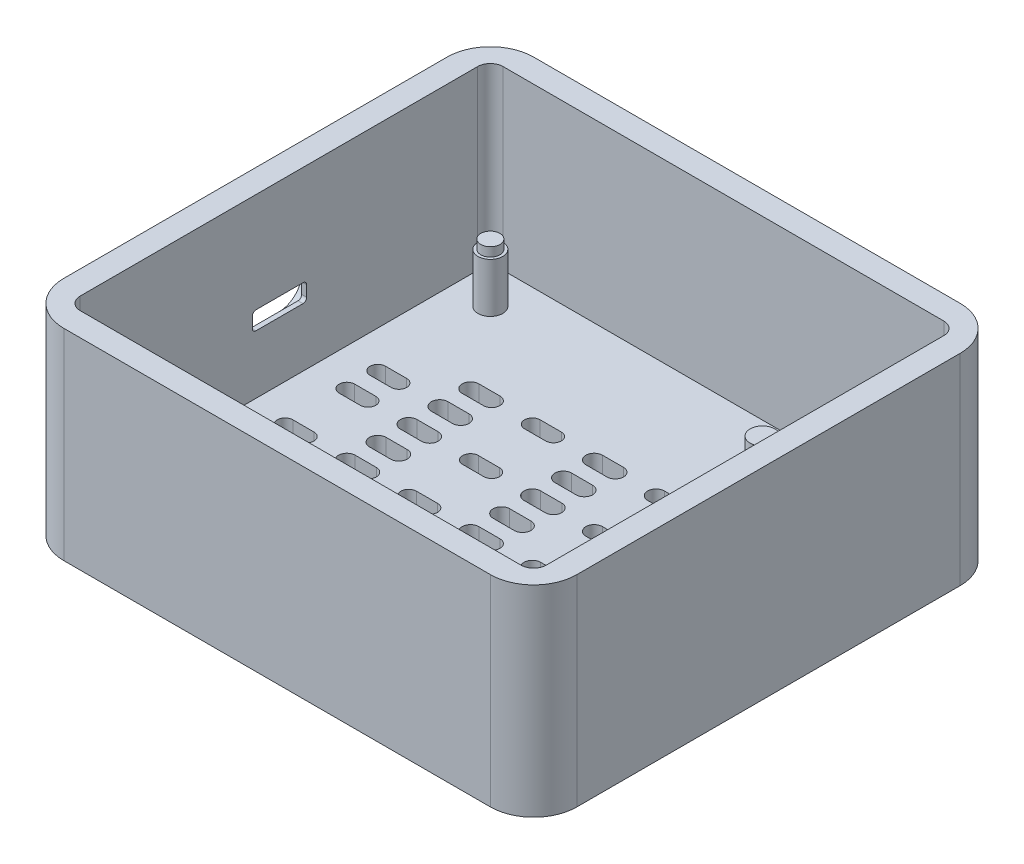
SolidWorks part; units mm, degrees
ref_plane "前视基准面" through (0, 0, 0) normal (0, 0, 1) x (1, 0, 0)
ref_plane "上视基准面" through (0, 0, 0) normal (0, 1, 0) x (1, 0, 0)
ref_plane "右视基准面" through (0, 0, 0) normal (1, 0, 0) x (0, 0, -1)
other "Configuration Table"
sketch "草图1" plane through (0, 0, 0) normal (0, 1, 0) x (1, 0, 0)
  line L1 (-34.5, 34) -> (34.5, 34)
  line L2 (-37.5, 31) -> (-37.5, -31)
  line L3 (-34.5, -34) -> (34.5, -34)
  line L4 (37.5, 31) -> (37.5, -31)
  line L5 (-37.5, 34) -> (37.5, -34) construction
  line L6 (-37.5, -34) -> (37.5, 34) construction
  arc A0 (-34.5, 34) -> (-37.5, 31) centre (-34.5, 31) ccw
  arc A1 (-37.5, -31) -> (-34.5, -34) centre (-34.5, -31) ccw
  arc A2 (34.5, -34) -> (37.5, -31) centre (34.5, -31) ccw
  arc A3 (34.5, 34) -> (37.5, 31) centre (34.5, 31) cw
  point P0 (0, 0)
  dimension "D3" = 3
  dimension "D4" = 3
  dimension "D1" = 75
  dimension "D2" = 68
extrude "凸台-拉伸1" add sketch "草图1" along normal blind 4
sketch "草图2" plane through (0, 4, 0) normal (0, 1, 0) x (1, 0, 0)
  line L0 (-1.709, 0) -> (1.709, 0) construction
  line L1 (-1.709, 1.3428) -> (1.709, 1.3428)
  line L2 (-1.709, -1.3428) -> (1.709, -1.3428)
  line L6 (18.291, 0) -> (21.709, 0) construction
  line L7 (18.291, 1.3428) -> (21.709, 1.3428)
  line L8 (18.291, -1.3428) -> (21.709, -1.3428)
  line L15 (-21.709, 0) -> (-18.291, 0) construction
  line L16 (-21.709, 1.3428) -> (-18.291, 1.3428)
  line L17 (-21.709, -1.3428) -> (-18.291, -1.3428)
  line L21 (-1.709, -5) -> (1.709, -5) construction
  line L22 (-1.709, -3.6572) -> (1.709, -3.6572)
  line L23 (-1.709, -6.3428) -> (1.709, -6.3428)
  line L24 (8.291, -5) -> (11.709, -5) construction
  line L25 (8.291, -3.6572) -> (11.709, -3.6572)
  line L26 (8.291, -6.3428) -> (11.709, -6.3428)
  line L27 (18.291, -5) -> (21.709, -5) construction
  line L28 (18.291, -3.6572) -> (21.709, -3.6572)
  line L29 (18.291, -6.3428) -> (21.709, -6.3428)
  line L30 (28.291, -5) -> (31.709, -5) construction
  line L31 (28.291, -3.6572) -> (31.709, -3.6572)
  line L32 (28.291, -6.3428) -> (31.709, -6.3428)
  line L33 (-11.709, -5) -> (-8.291, -5) construction
  line L34 (-11.709, -3.7386) -> (-8.291, -3.7386)
  line L35 (-11.709, -6.2614) -> (-8.291, -6.2614)
  line L36 (-21.709, -5) -> (-18.291, -5) construction
  line L37 (-21.709, -3.6572) -> (-18.291, -3.6572)
  line L38 (-21.709, -6.3428) -> (-18.291, -6.3428)
  line L39 (-31.709, -5) -> (-28.291, -5) construction
  line L40 (-31.709, -3.7386) -> (-28.291, -3.7386)
  line L41 (-31.709, -6.2614) -> (-28.291, -6.2614)
  line L42 (-1.709, -10) -> (1.709, -10) construction
  line L43 (-1.709, -8.6572) -> (1.709, -8.6572)
  line L44 (-1.709, -11.3428) -> (1.709, -11.3428)
  line L48 (18.291, -10) -> (21.709, -10) construction
  line L49 (18.291, -8.6572) -> (21.709, -8.6572)
  line L50 (18.291, -11.3428) -> (21.709, -11.3428)
  line L51 (28.291, -10) -> (31.709, -10) construction
  line L52 (28.291, -8.6572) -> (31.709, -8.6572)
  line L53 (28.291, -11.3428) -> (31.709, -11.3428)
  line L57 (-21.709, -10) -> (-18.291, -10) construction
  line L58 (-21.709, -8.6572) -> (-18.291, -8.6572)
  line L59 (-21.709, -11.3428) -> (-18.291, -11.3428)
  line L60 (-31.709, -10) -> (-28.291, -10) construction
  line L61 (-31.709, -8.7386) -> (-28.291, -8.7386)
  line L62 (-31.709, -11.2614) -> (-28.291, -11.2614)
  line L63 (-1.709, -15) -> (1.709, -15) construction
  line L64 (-1.709, -13.6572) -> (1.709, -13.6572)
  line L65 (-1.709, -16.3428) -> (1.709, -16.3428)
  line L66 (8.291, -15) -> (11.709, -15) construction
  line L67 (8.291, -13.6572) -> (11.709, -13.6572)
  line L68 (8.291, -16.3428) -> (11.709, -16.3428)
  line L69 (18.291, -15) -> (21.709, -15) construction
  line L70 (18.291, -13.6572) -> (21.709, -13.6572)
  line L71 (18.291, -16.3428) -> (21.709, -16.3428)
  line L75 (-11.709, -15) -> (-8.291, -15) construction
  line L76 (-11.709, -13.7386) -> (-8.291, -13.7386)
  line L77 (-11.709, -16.2614) -> (-8.291, -16.2614)
  line L78 (-21.709, -15) -> (-18.291, -15) construction
  line L79 (-21.709, -13.6572) -> (-18.291, -13.6572)
  line L80 (-21.709, -16.3428) -> (-18.291, -16.3428)
  line L84 (-1.709, 5) -> (1.709, 5) construction
  line L85 (-1.709, 6.3428) -> (1.709, 6.3428)
  line L86 (-1.709, 3.6572) -> (1.709, 3.6572)
  line L87 (8.291, 5) -> (11.709, 5) construction
  line L88 (8.291, 6.3428) -> (11.709, 6.3428)
  line L89 (8.291, 3.6572) -> (11.709, 3.6572)
  line L90 (18.291, 5) -> (21.709, 5) construction
  line L91 (18.291, 6.3428) -> (21.709, 6.3428)
  line L92 (18.291, 3.6572) -> (21.709, 3.6572)
  line L93 (28.291, 5) -> (31.709, 5) construction
  line L94 (28.291, 6.3428) -> (31.709, 6.3428)
  line L95 (28.291, 3.6572) -> (31.709, 3.6572)
  line L96 (-11.709, 5) -> (-8.291, 5) construction
  line L97 (-11.709, 6.2614) -> (-8.291, 6.2614)
  line L98 (-11.709, 3.7386) -> (-8.291, 3.7386)
  line L99 (-21.709, 5) -> (-18.291, 5) construction
  line L100 (-21.709, 6.3428) -> (-18.291, 6.3428)
  line L101 (-21.709, 3.6572) -> (-18.291, 3.6572)
  line L102 (-31.709, 5) -> (-28.291, 5) construction
  line L103 (-31.709, 6.2614) -> (-28.291, 6.2614)
  line L104 (-31.709, 3.7386) -> (-28.291, 3.7386)
  line L105 (-1.709, 10) -> (1.709, 10) construction
  line L106 (-1.709, 11.3428) -> (1.709, 11.3428)
  line L107 (-1.709, 8.6572) -> (1.709, 8.6572)
  line L111 (18.291, 10) -> (21.709, 10) construction
  line L112 (18.291, 11.3428) -> (21.709, 11.3428)
  line L113 (18.291, 8.6572) -> (21.709, 8.6572)
  line L114 (28.291, 10) -> (31.709, 10) construction
  line L115 (28.291, 11.3428) -> (31.709, 11.3428)
  line L116 (28.291, 8.6572) -> (31.709, 8.6572)
  line L120 (-21.709, 10) -> (-18.291, 10) construction
  line L121 (-21.709, 11.3428) -> (-18.291, 11.3428)
  line L122 (-21.709, 8.6572) -> (-18.291, 8.6572)
  line L123 (-31.709, 10) -> (-28.291, 10) construction
  line L124 (-31.709, 11.2614) -> (-28.291, 11.2614)
  line L125 (-31.709, 8.7386) -> (-28.291, 8.7386)
  line L126 (-1.709, 15) -> (1.709, 15) construction
  line L127 (-1.709, 16.3428) -> (1.709, 16.3428)
  line L128 (-1.709, 13.6572) -> (1.709, 13.6572)
  line L129 (8.291, 15) -> (11.709, 15) construction
  line L130 (8.291, 16.3428) -> (11.709, 16.3428)
  line L131 (8.291, 13.6572) -> (11.709, 13.6572)
  line L132 (18.291, 15) -> (21.709, 15) construction
  line L133 (18.291, 16.3428) -> (21.709, 16.3428)
  line L134 (18.291, 13.6572) -> (21.709, 13.6572)
  line L138 (-11.709, 15) -> (-8.291, 15) construction
  line L139 (-11.709, 16.2614) -> (-8.291, 16.2614)
  line L140 (-11.709, 13.7386) -> (-8.291, 13.7386)
  line L141 (-21.709, 15) -> (-18.291, 15) construction
  line L142 (-21.709, 16.3428) -> (-18.291, 16.3428)
  line L143 (-21.709, 13.6572) -> (-18.291, 13.6572)
  line L188 (28.291, 0) -> (31.709, 0) construction
  line L189 (28.291, 1.3428) -> (31.709, 1.3428)
  line L190 (28.291, -1.3428) -> (31.709, -1.3428)
  line L191 (8.291, 0) -> (11.709, 0) construction
  line L192 (8.291, 1.3428) -> (11.709, 1.3428)
  line L193 (8.291, -1.3428) -> (11.709, -1.3428)
  line L194 (-11.709, 0) -> (-8.291, 0) construction
  line L195 (-11.709, 1.3428) -> (-8.291, 1.3428)
  line L196 (-11.709, -1.3428) -> (-8.291, -1.3428)
  line L197 (-31.709, 0) -> (-28.291, 0) construction
  line L198 (-31.709, 1.3428) -> (-28.291, 1.3428)
  line L199 (-31.709, -1.3428) -> (-28.291, -1.3428)
  line L200 (28.291, 0) -> (31.709, 0) construction
  line L201 (28.291, 1.3428) -> (31.709, 1.3428)
  line L202 (28.291, -1.3428) -> (31.709, -1.3428)
  line L203 (8.291, 0) -> (11.709, 0) construction
  line L204 (8.291, 1.3428) -> (11.709, 1.3428)
  line L205 (8.291, -1.3428) -> (11.709, -1.3428)
  line L206 (-11.709, 0) -> (-8.291, 0) construction
  line L207 (-11.709, 1.3428) -> (-8.291, 1.3428)
  line L208 (-11.709, -1.3428) -> (-8.291, -1.3428)
  line L209 (-31.709, 0) -> (-28.291, 0) construction
  line L210 (-31.709, 1.3428) -> (-28.291, 1.3428)
  line L211 (-31.709, -1.3428) -> (-28.291, -1.3428)
  arc A0 (-1.709, 1.3428) -> (-1.709, -1.3428) centre (-1.709, 0) ccw
  arc A1 (1.709, -1.3428) -> (1.709, 1.3428) centre (1.709, 0) ccw
  arc A4 (18.291, 1.3428) -> (18.291, -1.3428) centre (18.291, 0) ccw
  arc A5 (21.709, -1.3428) -> (21.709, 1.3428) centre (21.709, 0) ccw
  arc A10 (-21.709, 1.3428) -> (-21.709, -1.3428) centre (-21.709, 0) ccw
  arc A11 (-18.291, -1.3428) -> (-18.291, 1.3428) centre (-18.291, 0) ccw
  arc A14 (-1.709, -3.6572) -> (-1.709, -6.3428) centre (-1.709, -5) ccw
  arc A15 (1.709, -6.3428) -> (1.709, -3.6572) centre (1.709, -5) ccw
  arc A16 (8.291, -3.6572) -> (8.291, -6.3428) centre (8.291, -5) ccw
  arc A17 (11.709, -6.3428) -> (11.709, -3.6572) centre (11.709, -5) ccw
  arc A18 (18.291, -3.6572) -> (18.291, -6.3428) centre (18.291, -5) ccw
  arc A19 (21.709, -6.3428) -> (21.709, -3.6572) centre (21.709, -5) ccw
  arc A20 (28.291, -3.6572) -> (28.291, -6.3428) centre (28.291, -5) ccw
  arc A21 (31.709, -6.3428) -> (31.709, -3.6572) centre (31.709, -5) ccw
  arc A22 (-11.709, -3.7386) -> (-11.709, -6.2614) centre (-11.709, -5) ccw
  arc A23 (-8.291, -6.2614) -> (-8.291, -3.7386) centre (-8.291, -5) ccw
  arc A24 (-21.709, -3.6572) -> (-21.709, -6.3428) centre (-21.709, -5) ccw
  arc A25 (-18.291, -6.3428) -> (-18.291, -3.6572) centre (-18.291, -5) ccw
  arc A26 (-31.709, -3.7386) -> (-31.709, -6.2614) centre (-31.709, -5) ccw
  arc A27 (-28.291, -6.2614) -> (-28.291, -3.7386) centre (-28.291, -5) ccw
  arc A28 (-1.709, -8.6572) -> (-1.709, -11.3428) centre (-1.709, -10) ccw
  arc A29 (1.709, -11.3428) -> (1.709, -8.6572) centre (1.709, -10) ccw
  arc A32 (18.291, -8.6572) -> (18.291, -11.3428) centre (18.291, -10) ccw
  arc A33 (21.709, -11.3428) -> (21.709, -8.6572) centre (21.709, -10) ccw
  arc A34 (28.291, -8.6572) -> (28.291, -11.3428) centre (28.291, -10) ccw
  arc A35 (31.709, -11.3428) -> (31.709, -8.6572) centre (31.709, -10) ccw
  arc A38 (-21.709, -8.6572) -> (-21.709, -11.3428) centre (-21.709, -10) ccw
  arc A39 (-18.291, -11.3428) -> (-18.291, -8.6572) centre (-18.291, -10) ccw
  arc A40 (-31.709, -8.7386) -> (-31.709, -11.2614) centre (-31.709, -10) ccw
  arc A41 (-28.291, -11.2614) -> (-28.291, -8.7386) centre (-28.291, -10) ccw
  arc A42 (-1.709, -13.6572) -> (-1.709, -16.3428) centre (-1.709, -15) ccw
  arc A43 (1.709, -16.3428) -> (1.709, -13.6572) centre (1.709, -15) ccw
  arc A44 (8.291, -13.6572) -> (8.291, -16.3428) centre (8.291, -15) ccw
  arc A45 (11.709, -16.3428) -> (11.709, -13.6572) centre (11.709, -15) ccw
  arc A46 (18.291, -13.6572) -> (18.291, -16.3428) centre (18.291, -15) ccw
  arc A47 (21.709, -16.3428) -> (21.709, -13.6572) centre (21.709, -15) ccw
  arc A50 (-11.709, -13.7386) -> (-11.709, -16.2614) centre (-11.709, -15) ccw
  arc A51 (-8.291, -16.2614) -> (-8.291, -13.7386) centre (-8.291, -15) ccw
  arc A52 (-21.709, -13.6572) -> (-21.709, -16.3428) centre (-21.709, -15) ccw
  arc A53 (-18.291, -16.3428) -> (-18.291, -13.6572) centre (-18.291, -15) ccw
  arc A56 (-1.709, 6.3428) -> (-1.709, 3.6572) centre (-1.709, 5) ccw
  arc A57 (1.709, 3.6572) -> (1.709, 6.3428) centre (1.709, 5) ccw
  arc A58 (8.291, 6.3428) -> (8.291, 3.6572) centre (8.291, 5) ccw
  arc A59 (11.709, 3.6572) -> (11.709, 6.3428) centre (11.709, 5) ccw
  arc A60 (18.291, 6.3428) -> (18.291, 3.6572) centre (18.291, 5) ccw
  arc A61 (21.709, 3.6572) -> (21.709, 6.3428) centre (21.709, 5) ccw
  arc A62 (28.291, 6.3428) -> (28.291, 3.6572) centre (28.291, 5) ccw
  arc A63 (31.709, 3.6572) -> (31.709, 6.3428) centre (31.709, 5) ccw
  arc A64 (-11.709, 6.2614) -> (-11.709, 3.7386) centre (-11.709, 5) ccw
  arc A65 (-8.291, 3.7386) -> (-8.291, 6.2614) centre (-8.291, 5) ccw
  arc A66 (-21.709, 6.3428) -> (-21.709, 3.6572) centre (-21.709, 5) ccw
  arc A67 (-18.291, 3.6572) -> (-18.291, 6.3428) centre (-18.291, 5) ccw
  arc A68 (-31.709, 6.2614) -> (-31.709, 3.7386) centre (-31.709, 5) ccw
  arc A69 (-28.291, 3.7386) -> (-28.291, 6.2614) centre (-28.291, 5) ccw
  arc A70 (-1.709, 11.3428) -> (-1.709, 8.6572) centre (-1.709, 10) ccw
  arc A71 (1.709, 8.6572) -> (1.709, 11.3428) centre (1.709, 10) ccw
  arc A74 (18.291, 11.3428) -> (18.291, 8.6572) centre (18.291, 10) ccw
  arc A75 (21.709, 8.6572) -> (21.709, 11.3428) centre (21.709, 10) ccw
  arc A76 (28.291, 11.3428) -> (28.291, 8.6572) centre (28.291, 10) ccw
  arc A77 (31.709, 8.6572) -> (31.709, 11.3428) centre (31.709, 10) ccw
  arc A80 (-21.709, 11.3428) -> (-21.709, 8.6572) centre (-21.709, 10) ccw
  arc A81 (-18.291, 8.6572) -> (-18.291, 11.3428) centre (-18.291, 10) ccw
  arc A82 (-31.709, 11.2614) -> (-31.709, 8.7386) centre (-31.709, 10) ccw
  arc A83 (-28.291, 8.7386) -> (-28.291, 11.2614) centre (-28.291, 10) ccw
  arc A84 (-1.709, 16.3428) -> (-1.709, 13.6572) centre (-1.709, 15) ccw
  arc A85 (1.709, 13.6572) -> (1.709, 16.3428) centre (1.709, 15) ccw
  arc A86 (8.291, 16.3428) -> (8.291, 13.6572) centre (8.291, 15) ccw
  arc A87 (11.709, 13.6572) -> (11.709, 16.3428) centre (11.709, 15) ccw
  arc A88 (18.291, 16.3428) -> (18.291, 13.6572) centre (18.291, 15) ccw
  arc A89 (21.709, 13.6572) -> (21.709, 16.3428) centre (21.709, 15) ccw
  arc A92 (-11.709, 16.2614) -> (-11.709, 13.7386) centre (-11.709, 15) ccw
  arc A93 (-8.291, 13.7386) -> (-8.291, 16.2614) centre (-8.291, 15) ccw
  arc A94 (-21.709, 16.3428) -> (-21.709, 13.6572) centre (-21.709, 15) ccw
  arc A95 (-18.291, 13.6572) -> (-18.291, 16.3428) centre (-18.291, 15) ccw
  arc A138 (28.291, 1.3428) -> (28.291, -1.3428) centre (28.291, 0) ccw
  arc A139 (31.709, -1.3428) -> (31.709, 1.3428) centre (31.709, 0) ccw
  arc A140 (8.291, 1.3428) -> (8.291, -1.3428) centre (8.291, 0) ccw
  arc A141 (11.709, -1.3428) -> (11.709, 1.3428) centre (11.709, 0) ccw
  arc A142 (-11.709, 1.3428) -> (-11.709, -1.3428) centre (-11.709, 0) ccw
  arc A143 (-8.291, -1.3428) -> (-8.291, 1.3428) centre (-8.291, 0) ccw
  arc A144 (-31.709, 1.3428) -> (-31.709, -1.3428) centre (-31.709, 0) ccw
  arc A145 (-28.291, -1.3428) -> (-28.291, 1.3428) centre (-28.291, 0) ccw
  point P2 (0, 0)
  point P12 (30, 0)
  point P19 (20, 0)
  point P33 (10, 0)
  point P40 (-20, 0)
  point P47 (-10, 0)
  point P53 (0, -5)
  point P60 (10, -5)
  point P67 (20, -5)
  point P74 (30, -5)
  point P81 (-10, -5)
  point P88 (-20, -5)
  point P95 (-30, -5)
  point P102 (0, -10)
  point P116 (20, -10)
  point P123 (30, -10)
  point P137 (-20, -10)
  point P144 (-30, -10)
  point P151 (0, -15)
  point P158 (10, -15)
  point P165 (20, -15)
  point P173 (-30, -15)
  point P179 (-10, -15)
  point P186 (-20, -15)
  point P194 (30, 15)
  point P200 (0, 5)
  point P207 (10, 5)
  point P214 (20, 5)
  point P221 (30, 5)
  point P228 (-10, 5)
  point P235 (-20, 5)
  point P242 (-30, 5)
  point P249 (0, 10)
  point P263 (20, 10)
  point P270 (30, 10)
  point P284 (-20, 10)
  point P291 (-30, 10)
  point P298 (0, 15)
  point P305 (10, 15)
  point P312 (20, 15)
  point P319 (-30, 0)
  point P326 (-10, 15)
  point P333 (-20, 15)
  point P340 (30, -15)
  point P346 (-30, 15)
  point P355 (30, 0)
  point P362 (10, 0)
  point P369 (-10, 0)
  point P376 (-30, 0)
  point P383 (30, 0)
  point P390 (10, 0)
  point P397 (-10, 0)
  point P404 (-30, 0)
  point P411 (30, 0)
  point P418 (10, 0)
  point P425 (-10, 0)
  point P432 (-30, 0)
  point P439 (30, 0)
  point P446 (10, 0)
  point P453 (-10, 0)
  point P460 (-30, 0)
  dimension "D1" = 4
  dimension "D2" = 4
  dimension "D3" = 4
  dimension "D4" = 4
extrude "切除-拉伸1" cut sketch "草图2" against normal blind 65
sketch "草图7" plane through (0, 4, 0) normal (0, 1, 0) x (1, 0, 0)
  line L1 (-36.6213, 33.1213) -> (-31.6213, 33.1213) construction
  line L2 (-36.6213, 33.1213) -> (-36.6213, 28.1213) construction
  line L3 (-36.6213, 28.1213) -> (-31.6213, 28.1213) construction
  line L4 (-31.6213, 33.1213) -> (-31.6213, 28.1213) construction
  line L5 (-36.6213, -33.1213) -> (-31.6213, -33.1213) construction
  line L6 (-36.6213, -33.1213) -> (-36.6213, -28.1213) construction
  line L7 (-36.6213, -28.1213) -> (-31.6213, -28.1213) construction
  line L8 (-31.6213, -33.1213) -> (-31.6213, -28.1213) construction
  arc A0 (-34.5, 34) -> (-37.5, 31) centre (-34.5, 31) ccw construction
  circle A1 centre (-31.6213, 28.1213) radius 2
  arc A2 (-37.5, -31) -> (-34.5, -34) centre (-34.5, -31) ccw construction
  circle A3 centre (-31.6213, -28.1213) radius 2
  dimension "D3" = 5
  dimension "D1" = 5
  dimension "D2" = 5
  dimension "D4" = 5
extrude "凸台-拉伸4" add sketch "草图7" along normal blind 8
sketch "草图8" plane through (0, 12, 0) normal (0, 1, 0) x (1, 0, 0)
  circle A0 centre (-31.6213, -28.1213) radius 1.55
extrude "凸台-拉伸5" add sketch "草图8" along normal blind 1.4618
sketch "草图9" plane through (0, 12, 0) normal (0, 1, 0) x (1, 0, 0)
  circle A0 centre (-31.6213, 28.1213) radius 1.55
extrude "凸台-拉伸6" add sketch "草图9" along normal blind 1.4512
sketch "草图10" plane through (0, 4, 0) normal (0, 1, 0) x (1, 0, 0)
  line L0 (37.5, -31) -> (37.5, 31) construction
  circle A0 centre (16.546, -27.0481) radius 2
  circle A1 centre (16.546, 23.9759) radius 2
  dimension "D1" = 20.954
  dimension "D2" = 20.954
extrude "凸台-拉伸7" add sketch "草图10" along normal blind 8
sketch "草图11" plane through (0, 0, 0) normal (0, -1, 0) x (1, 0, 0)
  line L4 (-34.5, -38) -> (34.5, -38)
  line L5 (41.5, -31) -> (41.5, 31)
  line L6 (34.5, 38) -> (-34.5, 38)
  line L7 (-41.5, 31) -> (-41.5, -31)
  line L8 (-34.5, -34) -> (34.5, -34)
  line L9 (37.5, -31) -> (37.5, 31)
  line L10 (34.5, 34) -> (-34.5, 34)
  line L11 (-37.5, 31) -> (-37.5, -31)
  line L12 (-34.5, -34) -> (34.5, -34)
  line L13 (37.5, -31) -> (37.5, 31)
  line L14 (34.5, 34) -> (-34.5, 34)
  line L15 (-37.5, 31) -> (-37.5, -31)
  arc A4 (-41.5, -31) -> (-34.5, -38) centre (-34.5, -31) ccw
  arc A5 (34.5, -38) -> (41.5, -31) centre (34.5, -31) ccw
  arc A6 (41.5, 31) -> (34.5, 38) centre (34.5, 31) ccw
  arc A7 (-34.5, 38) -> (-41.5, 31) centre (-34.5, 31) ccw
  arc A8 (-37.5, -31) -> (-34.5, -34) centre (-34.5, -31) ccw
  arc A9 (34.5, -34) -> (37.5, -31) centre (34.5, -31) ccw
  arc A10 (37.5, 31) -> (34.5, 34) centre (34.5, 31) ccw
  arc A11 (-34.5, 34) -> (-37.5, 31) centre (-34.5, 31) ccw
  arc A12 (-37.5, -31) -> (-34.5, -34) centre (-34.5, -31) ccw
  arc A13 (34.5, -34) -> (37.5, -31) centre (34.5, -31) ccw
  arc A14 (37.5, 31) -> (34.5, 34) centre (34.5, 31) ccw
  arc A15 (-34.5, 34) -> (-37.5, 31) centre (-34.5, 31) ccw
  dimension "D1" = 0
  dimension "D2" = 4
extrude "凸台-拉伸8" add sketch "草图11" against normal blind 28.55
sketch "草图12" plane through (-41.5, 0, 0) normal (-1, 0, 0) x (0, 0, 1)
  line L2 (-4.189, 9.55) -> (4.046, 9.55) construction
  line L4 (-3.8715, 9.55) -> (3.7285, 9.55)
  line L6 (-4.4715, 9.55) -> (4.3285, 9.55)
  line L7 (-4.4715, 10.15) -> (-4.4715, 11.8)
  line L8 (-3.8715, 12.4) -> (3.7285, 12.4)
  line L9 (4.3285, 10.15) -> (4.3285, 11.8)
  arc A0 (3.7285, 9.55) -> (4.3285, 10.15) centre (3.7285, 10.15) ccw
  arc A1 (-3.8715, 9.55) -> (-4.4715, 10.15) centre (-3.8715, 10.15) cw
  arc A2 (-3.8715, 12.4) -> (-4.4715, 11.8) centre (-3.8715, 11.8) ccw
  arc A3 (3.7285, 12.4) -> (4.3285, 11.8) centre (3.7285, 11.8) cw
  point P0 (-4.189, 9.55)
  point P1 (4.046, 9.55)
  point P13 (-0.0715, 9.55)
  dimension "D1" = 0.6
extrude "切除-拉伸2" cut sketch "草图12" against normal blind 9.55 contours A0 L9 A3 L8 A2 L7 A1 L4
sketch "草图13" plane through (-41.5, 0, 0) normal (-1, 0, 0) x (0, 0, 1)
  line L12 (3.7285, 14.4) -> (-3.8715, 14.4)
  line L13 (6.3285, 10.15) -> (6.3285, 11.8)
  line L14 (-3.8715, 7.55) -> (3.7285, 7.55)
  line L15 (-6.4715, 11.8) -> (-6.4715, 10.15)
  line L16 (3.7285, 14.4) -> (-3.8715, 14.4)
  line L17 (6.3285, 10.15) -> (6.3285, 11.8)
  line L18 (-3.8715, 7.55) -> (3.7285, 7.55)
  line L19 (-6.4715, 11.8) -> (-6.4715, 10.15)
  arc A8 (-3.8715, 14.4) -> (-6.4715, 11.8) centre (-3.8715, 11.8) ccw
  arc A9 (6.3285, 11.8) -> (3.7285, 14.4) centre (3.7285, 11.8) ccw
  arc A10 (3.7285, 7.55) -> (6.3285, 10.15) centre (3.7285, 10.15) ccw
  arc A11 (-6.4715, 10.15) -> (-3.8715, 7.55) centre (-3.8715, 10.15) ccw
  arc A12 (-3.8715, 14.4) -> (-6.4715, 11.8) centre (-3.8715, 11.8) ccw
  arc A13 (6.3285, 11.8) -> (3.7285, 14.4) centre (3.7285, 11.8) ccw
  arc A14 (3.7285, 7.55) -> (6.3285, 10.15) centre (3.7285, 10.15) ccw
  arc A15 (-6.4715, 10.15) -> (-3.8715, 7.55) centre (-3.8715, 10.15) ccw
  point P0 (-6.4715, 10.975)
  point P1 (6.3285, 10.975)
  dimension "D2" = 12.8
  dimension "D1" = 2
extrude "切除-拉伸3" cut sketch "草图13" against normal blind 3 contours A12 L19 A15 L18 A14 L17 A13 L16
sketch "草图14" plane through (0, 28.55, 0) normal (0, 1, 0) x (1, 0, 0)
  line L0 (37.5, -31) -> (34.5, -31)
  line L1 (34.5, -31) -> (34.5, -34)
  line L2 (34.5, -34) -> (-34.5, -34) construction
  arc A0 (34.5, -34) -> (37.5, -31) centre (34.5, -31) ccw construction
sketch "草图15" plane through (0, 28.55, 0) normal (0, 1, 0) x (1, 0, 0)
  line L0 (-37.5, 31) -> (-37.5, 32.15)
  line L1 (-32.3505, 34) -> (-35.65, 34)
  line L2 (34.5, 34) -> (-34.5, 34) construction
  line L5 (-34.5, -31) -> (-37.5, -31)
  line L6 (-34.5, -31) -> (-34.5, -34)
  line L7 (-34.5, -34) -> (-35.65, -34)
  line L8 (-37.5, 31) -> (-37.5, -31)
  line L9 (-34.5, -34) -> (34.5, -34)
  line L10 (37.5, -31) -> (37.5, 31)
  line L11 (34.5, 34) -> (-34.5, 34)
  line L12 (-37.5, 31) -> (-37.5, -31)
  line L13 (-34.5, -34) -> (34.5, -34)
  line L14 (37.5, -31) -> (37.5, 31)
  line L15 (34.5, 34) -> (-34.5, 34)
  line L16 (-37.5, -31) -> (-37.5, -32.15)
  line L17 (34.5, -31) -> (37.5, -31)
  line L18 (34.5, -31) -> (34.5, -34)
  line L19 (34.5, -34) -> (35.65, -34)
  line L20 (37.5, -31) -> (37.5, -32.15)
  line L21 (34.5, 31) -> (37.5, 31)
  line L22 (34.5, 31) -> (34.5, 34)
  line L23 (34.5, 34) -> (35.65, 34)
  line L24 (37.5, 31) -> (37.5, 32.15)
  arc A0 (-35.65, -34) -> (-37.5, -32.15) centre (-35.65, -32.15) cw
  arc A1 (35.65, -34) -> (37.5, -32.15) centre (35.65, -32.15) ccw
  arc A2 (35.65, 34) -> (37.5, 32.15) centre (35.65, 32.15) cw
  arc A3 (-35.65, 34) -> (-37.5, 32.15) centre (-35.65, 32.15) ccw
  arc A4 (-34.5, 34) -> (-37.5, 31) centre (-34.5, 31) ccw
  arc A5 (-37.5, -31) -> (-34.5, -34) centre (-34.5, -31) ccw
  arc A6 (34.5, -34) -> (37.5, -31) centre (34.5, -31) ccw
  arc A7 (37.5, 31) -> (34.5, 34) centre (34.5, 31) ccw
  arc A8 (-34.5, 34) -> (-37.5, 31) centre (-34.5, 31) ccw
  arc A9 (-37.5, -31) -> (-34.5, -34) centre (-34.5, -31) ccw
  arc A10 (34.5, -34) -> (37.5, -31) centre (34.5, -31) ccw
  arc A11 (37.5, 31) -> (34.5, 34) centre (34.5, 31) ccw
  point P20 (-37.5, 33.9897)
  arc M10 (-37.5, 31) -> (-34.5, 34) centre (-34.5, 31) cw
  arc M12 (34.5, 34) -> (37.5, 31) centre (34.5, 31) cw
  arc M14 (37.5, -31) -> (34.5, -34) centre (34.5, -31) cw
  arc M16 (-34.5, -34) -> (-37.5, -31) centre (-34.5, -31) cw
  dimension "D2" = 1.85
  dimension "D1" = 0
extrude "切除-拉伸4" cut sketch "草图15" against normal up to surface (24.55 mm away) contours A0 L7 L16 M16 | L19 A1 L20 M14 | L1 A3 L0 M10 | A2 L23 L24 M12 up to face at (16.546, 4, -21.9759)
sketch "草图16" plane through (-38.5, 0, 0) normal (-1, 0, 0) x (0, 0, 1)
  line L0 (3.7285, 9.55) -> (-3.8715, 9.55) construction
  line L1 (-3.8715, 9.55) -> (3.7285, 9.55)
  line L2 (-3.8715, 9.55) -> (-3.8715, 9.4642)
  line L3 (-3.8715, 9.4642) -> (3.7285, 9.4642)
  line L4 (3.7285, 9.55) -> (3.7285, 9.4642)
  line L5 (4.3285, 10.15) -> (4.3285, 10.0642)
  line L6 (-4.4715, 10.15) -> (-4.4715, 10.0642)
  arc A0 (-4.4715, 10.15) -> (-3.8715, 9.55) centre (-3.8715, 10.15) ccw construction
  arc A1 (-3.8715, 9.4642) -> (-4.4715, 10.0642) centre (-3.8715, 10.0642) cw
  arc A2 (3.7285, 9.4642) -> (4.3285, 10.0642) centre (3.7285, 10.0642) ccw
  arc A3 (3.7285, 9.55) -> (4.3285, 10.15) centre (3.7285, 10.15) ccw construction
  arc A10 (3.7285, 9.55) -> (4.3285, 10.15) centre (3.7285, 10.15) ccw
  arc A11 (-4.4715, 10.15) -> (-3.8715, 9.55) centre (-3.8715, 10.15) ccw
  arc A12 (3.7285, 9.4642) -> (4.3285, 10.0642) centre (3.7285, 10.0642) ccw
  arc A13 (3.7285, 9.4642) -> (4.3285, 10.0642) centre (3.7285, 10.0642) ccw
  arc A14 (3.7285, 9.55) -> (4.3285, 10.15) centre (3.7285, 10.15) ccw
  arc A15 (-4.4715, 10.15) -> (-3.8715, 9.55) centre (-3.8715, 10.15) ccw
  line M15 (3.7285, 9.55) -> (-3.8715, 9.55)
  arc M16 (-3.8715, 9.55) -> (-4.4715, 10.15) centre (-3.8715, 10.15) cw
  arc M22 (4.3285, 10.15) -> (3.7285, 9.55) centre (3.7285, 10.15) cw
  dimension "D1" = 0
  dimension "D2" = 0
  dimension "D3" = 0
extrude "切除-拉伸5" cut sketch "草图16" against normal blind 32 contours L4 L2 L3 M15 | A1 L2 L6 M16 | L4 A2 L5 M22
sketch "草图18" plane through (0, 0, 0) normal (0, -1, 0) x (1, 0, 0)
  line L4 (-34.5, -38) -> (34.5, -38)
  line L5 (41.5, -31) -> (41.5, 31)
  line L6 (34.5, 38) -> (-34.5, 38)
  line L7 (-41.5, 31) -> (-41.5, -31)
  line L8 (-34.5, -38) -> (34.5, -38)
  line L9 (41.5, -31) -> (41.5, 31)
  line L10 (34.5, 38) -> (-34.5, 38)
  line L11 (-41.5, 31) -> (-41.5, -31)
  arc A4 (-41.5, -31) -> (-34.5, -38) centre (-34.5, -31) ccw
  arc A5 (34.5, -38) -> (41.5, -31) centre (34.5, -31) ccw
  arc A6 (41.5, 31) -> (34.5, 38) centre (34.5, 31) ccw
  arc A7 (-34.5, 38) -> (-41.5, 31) centre (-34.5, 31) ccw
  arc A8 (-41.5, -31) -> (-34.5, -38) centre (-34.5, -31) ccw
  arc A9 (34.5, -38) -> (41.5, -31) centre (34.5, -31) ccw
  arc A10 (41.5, 31) -> (34.5, 38) centre (34.5, 31) ccw
  arc A11 (-34.5, 38) -> (-41.5, 31) centre (-34.5, 31) ccw
  point P0 (-41.5, 31)
  dimension "D1" = 0
sketch "草图19" plane through (-41.5, 0, 0) normal (-1, 0, 0) x (0, 0, 1)
  line L0 (-4.4715, 11.8) -> (-4.4715, 10.0642) construction
  line L1 (-3.8715, 9.4642) -> (3.7285, 9.4642) construction
  line L2 (3.7285, 12.4) -> (-3.8715, 12.4) construction
  line L3 (4.3285, 11.8) -> (4.3285, 10.0642) construction
  line L4 (-4.4715, 11.8) -> (-4.4715, 10.0642)
  line L5 (-3.8715, 9.4642) -> (3.7285, 9.4642)
  line L6 (3.7285, 12.4) -> (-3.8715, 12.4)
  line L7 (4.3285, 11.8) -> (4.3285, 10.0642)
  line L8 (-4.4836, 15.8) -> (-4.4836, 14.0642)
  line L9 (-3.8836, 13.4642) -> (3.7164, 13.4642)
  line L10 (3.7164, 16.4) -> (-3.8836, 16.4)
  line L11 (4.3164, 15.8) -> (4.3164, 14.0642)
  arc A0 (-3.8715, 12.4) -> (-4.4715, 11.8) centre (-3.8715, 11.8) ccw construction
  arc A1 (-4.4715, 10.0642) -> (-3.8715, 9.4642) centre (-3.8715, 10.0642) ccw construction
  arc A2 (3.7285, 9.4642) -> (4.3285, 10.0642) centre (3.7285, 10.0642) ccw construction
  arc A3 (4.3285, 11.8) -> (3.7285, 12.4) centre (3.7285, 11.8) ccw construction
  arc A4 (-3.8715, 12.4) -> (-4.4715, 11.8) centre (-3.8715, 11.8) ccw
  arc A5 (-4.4715, 10.0642) -> (-3.8715, 9.4642) centre (-3.8715, 10.0642) ccw
  arc A6 (3.7285, 9.4642) -> (4.3285, 10.0642) centre (3.7285, 10.0642) ccw
  arc A7 (4.3285, 11.8) -> (3.7285, 12.4) centre (3.7285, 11.8) ccw
  arc A8 (-3.8836, 16.4) -> (-4.4836, 15.8) centre (-3.8836, 15.8) ccw
  arc A9 (-4.4836, 14.0642) -> (-3.8836, 13.4642) centre (-3.8836, 14.0642) ccw
  arc A10 (3.7164, 13.4642) -> (4.3164, 14.0642) centre (3.7164, 14.0642) ccw
  arc A11 (4.3164, 15.8) -> (3.7164, 16.4) centre (3.7164, 15.8) ccw
  dimension "D1" = 4
  dimension "D2" = 0.0121
extrude "切除-拉伸7" cut sketch "草图19" against normal blind 32 contours L8 A9 L9 A10 L11 A11 L10 A8
sketch "草图21" plane through (0, 28.55, 0) normal (0, 1, 0) x (1, 0, 0)
  line L0 (-35.65, 34) -> (35.65, 34) construction
  line L1 (-37.5, -32.15) -> (-37.5, 32.15) construction
  line L3 (-35.65, -34) -> (35.65, -34) construction
  line L4 (-41.5, 31) -> (-41.5, -31)
  line L5 (-34.5, -38) -> (34.5, -38)
  line L6 (41.5, -31) -> (41.5, 31)
  line L7 (34.5, 38) -> (-34.5, 38)
  line L8 (-41.5, 31) -> (-41.5, -31)
  line L9 (-34.5, -38) -> (34.5, -38)
  line L10 (41.5, -31) -> (41.5, 31)
  line L11 (34.5, 38) -> (-34.5, 38)
  line L12 (37.5, -32.15) -> (37.5, 32.15) construction
  line L13 (-35.65, -34) -> (35.65, -34)
  line L14 (-37.5, -32.15) -> (-37.5, 32.15)
  line L15 (37.5, -32.15) -> (37.5, 32.15)
  line L16 (-35.65, 34) -> (35.65, 34)
  arc A0 (-35.65, 34) -> (-37.5, 32.15) centre (-35.65, 32.15) ccw construction
  arc A1 (37.5, 32.15) -> (35.65, 34) centre (35.65, 32.15) ccw construction
  arc A2 (35.65, -34) -> (37.5, -32.15) centre (35.65, -32.15) ccw construction
  arc A3 (-37.5, -32.15) -> (-35.65, -34) centre (-35.65, -32.15) ccw construction
  arc A4 (-34.5, 38) -> (-41.5, 31) centre (-34.5, 31) ccw
  arc A5 (-41.5, -31) -> (-34.5, -38) centre (-34.5, -31) ccw
  arc A6 (34.5, -38) -> (41.5, -31) centre (34.5, -31) ccw
  arc A7 (41.5, 31) -> (34.5, 38) centre (34.5, 31) ccw
  arc A8 (-34.5, 38) -> (-41.5, 31) centre (-34.5, 31) ccw
  arc A9 (-41.5, -31) -> (-34.5, -38) centre (-34.5, -31) ccw
  arc A10 (34.5, -38) -> (41.5, -31) centre (34.5, -31) ccw
  arc A11 (41.5, 31) -> (34.5, 38) centre (34.5, 31) ccw
  arc A12 (35.65, -34) -> (37.5, -32.15) centre (35.65, -32.15) ccw
  arc A13 (-37.5, -32.15) -> (-35.65, -34) centre (-35.65, -32.15) ccw
  arc A14 (-35.65, 34) -> (-37.5, 32.15) centre (-35.65, 32.15) ccw
  arc A15 (37.5, 32.15) -> (35.65, 34) centre (35.65, 32.15) ccw
  dimension "D1" = 0
extrude "凸台-拉伸9" add sketch "草图21" along normal blind 4
sketch "草图22" plane through (-41.5, 0, 0) normal (-1, 0, 0) x (0, 0, 1)
  line L0 (4.3164, 14.3327) -> (4.3164, 14.0642) construction
  line L1 (6.3285, 10.15) -> (6.3285, 11.8) construction
  line L2 (-3.8715, 7.55) -> (3.7285, 7.55) construction
  line L3 (-6.4715, 11.8) -> (-6.4715, 10.15) construction
  line L4 (-4.4836, 14.3269) -> (-4.4836, 14.0642) construction
  line L5 (-3.8836, 13.4642) -> (3.7164, 13.4642) construction
  line L6 (4.3164, 14.3327) -> (4.3164, 14.0642)
  line L7 (6.3285, 10.15) -> (6.3285, 11.8)
  line L8 (-3.8715, 7.55) -> (3.7285, 7.55)
  line L9 (-6.4715, 11.8) -> (-6.4715, 10.15)
  line L10 (-4.4836, 14.3269) -> (-4.4836, 14.0642)
  line L11 (-3.8836, 13.4642) -> (3.7164, 13.4642)
  arc A0 (3.7164, 13.4642) -> (4.3164, 14.0642) centre (3.7164, 14.0642) ccw construction
  arc A1 (6.3285, 11.8) -> (4.3164, 14.3327) centre (3.7285, 11.8) ccw construction
  arc A2 (3.7285, 7.55) -> (6.3285, 10.15) centre (3.7285, 10.15) ccw construction
  arc A3 (-6.4715, 10.15) -> (-3.8715, 7.55) centre (-3.8715, 10.15) ccw construction
  arc A4 (-4.4836, 14.3269) -> (-6.4715, 11.8) centre (-3.8715, 11.8) ccw construction
  arc A5 (-4.4836, 14.0642) -> (-3.8836, 13.4642) centre (-3.8836, 14.0642) ccw construction
  arc A6 (3.7164, 13.4642) -> (4.3164, 14.0642) centre (3.7164, 14.0642) ccw
  arc A7 (6.3285, 11.8) -> (4.3164, 14.3327) centre (3.7285, 11.8) ccw
  arc A8 (3.7285, 7.55) -> (6.3285, 10.15) centre (3.7285, 10.15) ccw
  arc A9 (-6.4715, 10.15) -> (-3.8715, 7.55) centre (-3.8715, 10.15) ccw
  arc A10 (-4.4836, 14.3269) -> (-6.4715, 11.8) centre (-3.8715, 11.8) ccw
  arc A11 (-4.4836, 14.0642) -> (-3.8836, 13.4642) centre (-3.8836, 14.0642) ccw
extrude "凸台-拉伸10" add sketch "草图22" against normal blind 4 from surface at 0 starting at face at (-41.5, 16.275, 0)
sketch "草图23" plane through (-41.5, 0, 0) normal (-1, 0, 0) x (0, 0, 1)
  line L0 (4.3164, 15.8) -> (4.3164, 14.0642) construction
  line L1 (-3.8836, 13.4642) -> (3.7164, 13.4642) construction
  line L2 (-4.4836, 15.8) -> (-4.4836, 14.0642) construction
  line L3 (3.7164, 16.4) -> (-3.8836, 16.4) construction
  line L4 (4.3164, 15.8) -> (4.3164, 14.0642)
  line L5 (-3.8836, 13.4642) -> (3.7164, 13.4642)
  line L6 (-4.4836, 15.8) -> (-4.4836, 14.0642)
  line L7 (3.7164, 16.4) -> (-3.8836, 16.4)
  line L8 (7.3164, 15.8) -> (7.3164, 14.0642)
  line L9 (-3.8836, 10.4642) -> (3.7164, 10.4642)
  line L10 (-7.4836, 15.8) -> (-7.4836, 14.0642)
  line L11 (3.7164, 19.4) -> (-3.8836, 19.4)
  arc A0 (4.3164, 15.8) -> (3.7164, 16.4) centre (3.7164, 15.8) ccw construction
  arc A1 (3.7164, 13.4642) -> (4.3164, 14.0642) centre (3.7164, 14.0642) ccw construction
  arc A2 (-4.4836, 14.0642) -> (-3.8836, 13.4642) centre (-3.8836, 14.0642) ccw construction
  arc A3 (-3.8836, 16.4) -> (-4.4836, 15.8) centre (-3.8836, 15.8) ccw construction
  arc A4 (4.3164, 15.8) -> (3.7164, 16.4) centre (3.7164, 15.8) ccw
  arc A5 (3.7164, 13.4642) -> (4.3164, 14.0642) centre (3.7164, 14.0642) ccw
  arc A6 (-4.4836, 14.0642) -> (-3.8836, 13.4642) centre (-3.8836, 14.0642) ccw
  arc A7 (-3.8836, 16.4) -> (-4.4836, 15.8) centre (-3.8836, 15.8) ccw
  arc A8 (3.7164, 10.4642) -> (7.3164, 14.0642) centre (3.7164, 14.0642) ccw
  arc A9 (-7.4836, 14.0642) -> (-3.8836, 10.4642) centre (-3.8836, 14.0642) ccw
  arc A10 (-3.8836, 19.4) -> (-7.4836, 15.8) centre (-3.8836, 15.8) ccw
  arc A11 (7.3164, 15.8) -> (3.7164, 19.4) centre (3.7164, 15.8) ccw
  dimension "D1" = 3
extrude "切除-拉伸9" cut sketch "草图23" against normal blind 2.7
sketch "草图25" plane through (0, 32.55, 0) normal (0, 1, 0) x (1, 0, 0)
  line L0 (35.65, 34) -> (-35.65, 34) construction
  line L1 (-37.5, 32.15) -> (-37.5, -32.15) construction
  line L2 (-35.65, -34) -> (35.65, -34) construction
  line L3 (-35.65, -34) -> (35.65, -34) construction
  line L4 (37.5, -32.15) -> (37.5, 32.15) construction
  line L5 (35.65, 34) -> (-35.65, 34)
  line L6 (-37.5, 32.15) -> (-37.5, -32.15)
  line L7 (-35.65, -34) -> (35.65, -34)
  line L8 (-35.65, -34) -> (35.65, -34)
  line L9 (37.5, -32.15) -> (37.5, 32.15)
  line L10 (37.7, -32.15) -> (37.7, 32.15)
  line L11 (35.65, 34.2) -> (-35.65, 34.2)
  line L12 (-37.7, 32.15) -> (-37.7, -32.15)
  line L13 (-35.65, -34.2) -> (35.65, -34.2)
  arc A0 (37.5, 32.15) -> (35.65, 34) centre (35.65, 32.15) ccw construction
  arc A1 (-35.65, 34) -> (-37.5, 32.15) centre (-35.65, 32.15) ccw construction
  arc A2 (-37.5, -32.15) -> (-35.65, -34) centre (-35.65, -32.15) ccw construction
  arc A3 (35.65, -34) -> (37.5, -32.15) centre (35.65, -32.15) ccw construction
  arc A4 (37.5, 32.15) -> (35.65, 34) centre (35.65, 32.15) ccw
  arc A5 (-35.65, 34) -> (-37.5, 32.15) centre (-35.65, 32.15) ccw
  arc A6 (-37.5, -32.15) -> (-35.65, -34) centre (-35.65, -32.15) ccw
  arc A7 (35.65, -34) -> (37.5, -32.15) centre (35.65, -32.15) ccw
  arc A8 (35.65, -34.2) -> (37.7, -32.15) centre (35.65, -32.15) ccw
  arc A9 (37.7, 32.15) -> (35.65, 34.2) centre (35.65, 32.15) ccw
  arc A10 (-35.65, 34.2) -> (-37.7, 32.15) centre (-35.65, 32.15) ccw
  arc A11 (-37.7, -32.15) -> (-35.65, -34.2) centre (-35.65, -32.15) ccw
  line M13 (-37.5, -32.15) -> (-37.5, 32.15)
  arc M14 (-37.5, 32.15) -> (-35.65, 34) centre (-35.65, 32.15) cw
  line M15 (-35.65, 34) -> (35.65, 34)
  arc M16 (35.65, 34) -> (37.5, 32.15) centre (35.65, 32.15) cw
  line M17 (37.5, 32.15) -> (37.5, -32.15)
  arc M18 (37.5, -32.15) -> (35.65, -34) centre (35.65, -32.15) cw
  line M19 (35.65, -34) -> (-35.65, -34)
  arc M20 (-35.65, -34) -> (-37.5, -32.15) centre (-35.65, -32.15) cw
  dimension "D1" = 0.2
extrude "切除-拉伸10" cut sketch "草图25" against normal up to surface (28.55 mm away) contours L12 A11 L13 A8 L10 A9 L11 A10 M20 M13 M14 M15 M16 M17 M18 M19 up to face at (16.546, 4, -21.9759)
sketch "草图26" plane through (-38.8, 0, 0) normal (-1, 0, 0) x (0, 0, 1)
  line L4 (3.7164, 19.4) -> (-3.8836, 19.4)
  line L5 (-7.4836, 15.8) -> (-7.4836, 14.0642)
  line L6 (-3.8836, 10.4642) -> (3.7164, 10.4642)
  line L7 (7.3164, 14.0642) -> (7.3164, 15.8)
  line L8 (3.7164, 19.4) -> (-3.8836, 19.4)
  line L9 (-7.4836, 15.8) -> (-7.4836, 14.0642)
  line L10 (-3.8836, 10.4642) -> (3.7164, 10.4642)
  line L11 (7.3164, 14.0642) -> (7.3164, 15.8)
  arc A4 (7.3164, 15.8) -> (3.7164, 19.4) centre (3.7164, 15.8) ccw
  arc A5 (-3.8836, 19.4) -> (-7.4836, 15.8) centre (-3.8836, 15.8) ccw
  arc A6 (-7.4836, 14.0642) -> (-3.8836, 10.4642) centre (-3.8836, 14.0642) ccw
  arc A7 (3.7164, 10.4642) -> (7.3164, 14.0642) centre (3.7164, 14.0642) ccw
  arc A8 (7.3164, 15.8) -> (3.7164, 19.4) centre (3.7164, 15.8) ccw
  arc A9 (-3.8836, 19.4) -> (-7.4836, 15.8) centre (-3.8836, 15.8) ccw
  arc A10 (-7.4836, 14.0642) -> (-3.8836, 10.4642) centre (-3.8836, 14.0642) ccw
  arc A11 (3.7164, 10.4642) -> (7.3164, 14.0642) centre (3.7164, 14.0642) ccw
  dimension "D1" = 0
extrude "切除-拉伸11" cut sketch "草图26" against normal blind 0.3
